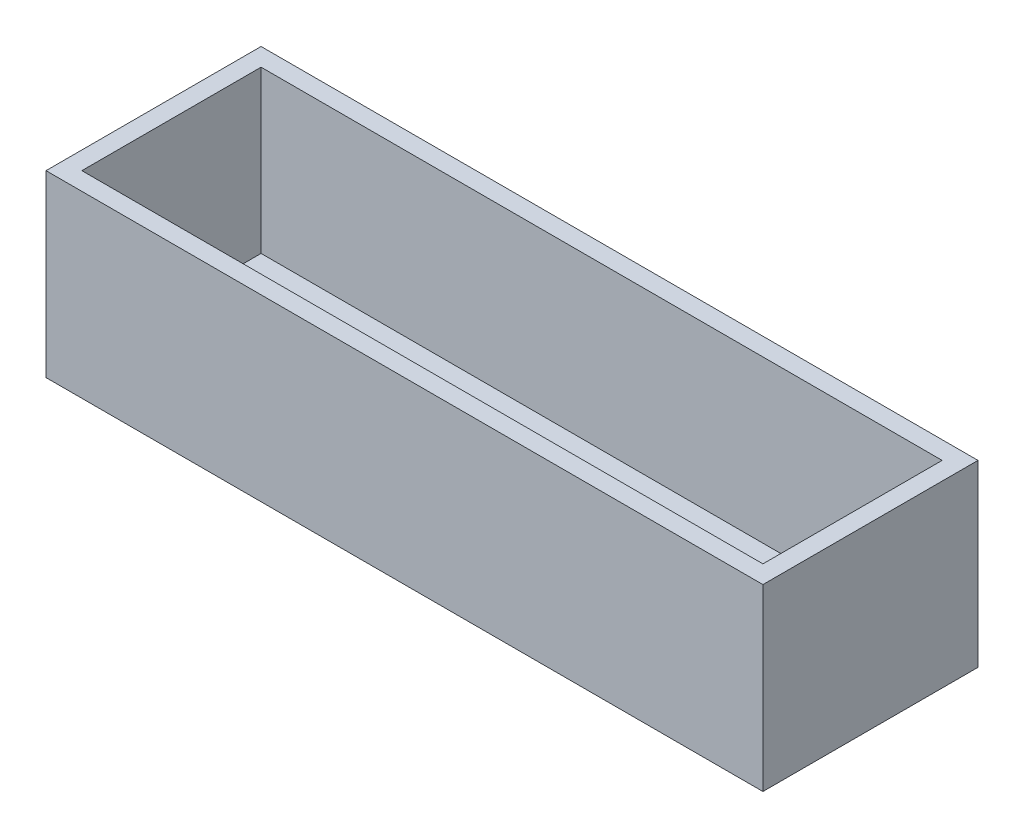
SolidWorks part; units mm, degrees
ref_plane "Front Plane" through (0, 0, 0) normal (0, 0, 1) x (1, 0, 0)
ref_plane "Top Plane" through (0, 0, 0) normal (0, 1, 0) x (1, 0, 0)
ref_plane "Right Plane" through (0, 0, 0) normal (1, 0, 0) x (0, 0, -1)
sketch "Sketch1" plane through (0, 0, 0) normal (0, 1, 0) x (1, 0, 0)
  line L1 (0, 0) -> (200, 0)
  line L2 (0, 0) -> (0, 60)
  line L3 (0, 60) -> (200, 60)
  line L4 (200, 0) -> (200, 60)
  dimension "D1" = 200
  dimension "D2" = 60
extrude "Boss-Extrude1" add sketch "Sketch1" along normal blind 50
shell "Shell1" thickness 5
